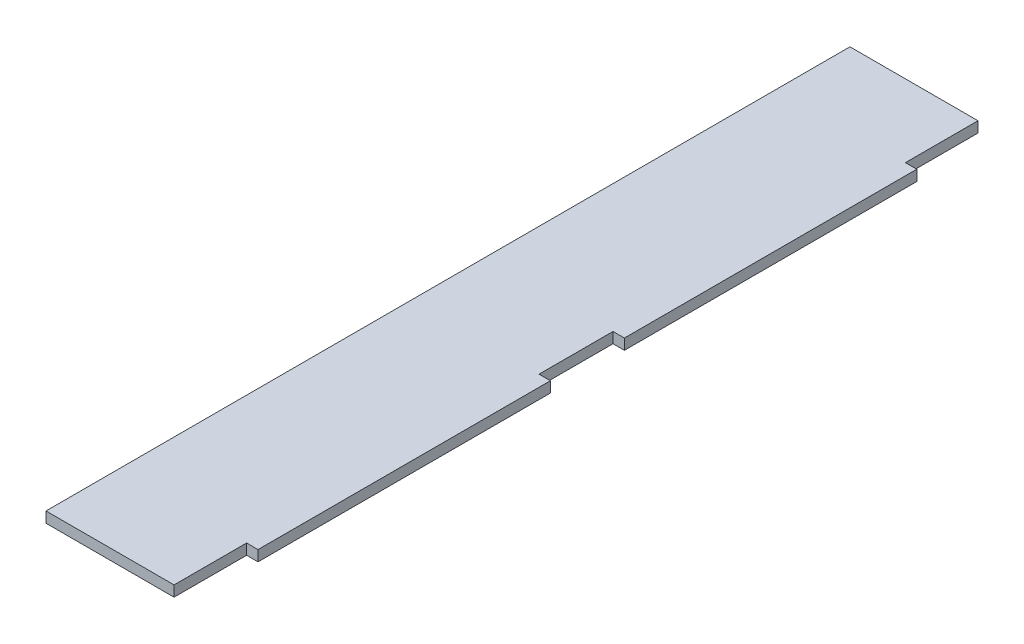
SolidWorks part; units mm, degrees
ref_plane "Front Plane" through (0, 0, 0) normal (0, 0, 1) x (1, 0, 0)
ref_plane "Top Plane" through (0, 0, 0) normal (0, 1, 0) x (1, 0, 0)
ref_plane "Right Plane" through (0, 0, 0) normal (1, 0, 0) x (0, 0, -1)
sketch "Sketch1" plane through (0, 0, 0) normal (0, 1, 0) x (1, 0, 0)
  line L0 (18, 113) -> (18, 102.8)
  line L2 (0, 0) -> (0, 113)
  line L5 (18, 102.8) -> (19.6, 102.8)
  line L6 (19.6, 102.8) -> (19.6, 61.7)
  line L7 (19.6, 61.7) -> (18, 61.7)
  line L8 (18, 61.7) -> (18, 51.3)
  line L9 (18, 51.3) -> (19.6, 51.3)
  line L10 (19.6, 51.3) -> (19.6, 10.2)
  line L11 (19.6, 10.2) -> (18, 10.2)
  line L12 (18, 10.2) -> (18, 0)
  line L13 (18, 0) -> (0, 0)
  line L14 (18, 113) -> (0, 113)
  point P1 (0, 0)
  point P7 (0, 0)
  point P16 (0, 0)
  dimension "D1" = 113
  dimension "D2" = 1.6
  dimension "D3" = 10.2
  dimension "D4" = 10.4
  dimension "D5" = 10.2
  dimension "D6" = 18
extrude "Boss-Extrude1" add sketch "Sketch1" along normal blind 1.5
equation "\"margin\"= 0.2"
equation "\"D3@Sketch1\"=\"tabwidth\" + \"margin\""
equation "\"D4@Sketch1\"=\"tabwidth\" + ( 2 * \"margin\" )"
equation "\"height\"= 18"
equation "\"length\"= 113"
equation "\"tabwidth\"= 10"
equation "\"width\"= 57"
equation "\"D1@Sketch1\"=\"length\""
equation "\"D6@Sketch1\"=\"height\""
equation "\"thick\"= 1.5"
equation "\"D2@Sketch1\"=\"thick\"+(\"margin\"/2)"
equation "\"D1@Boss-Extrude1\"=\"thick\""
